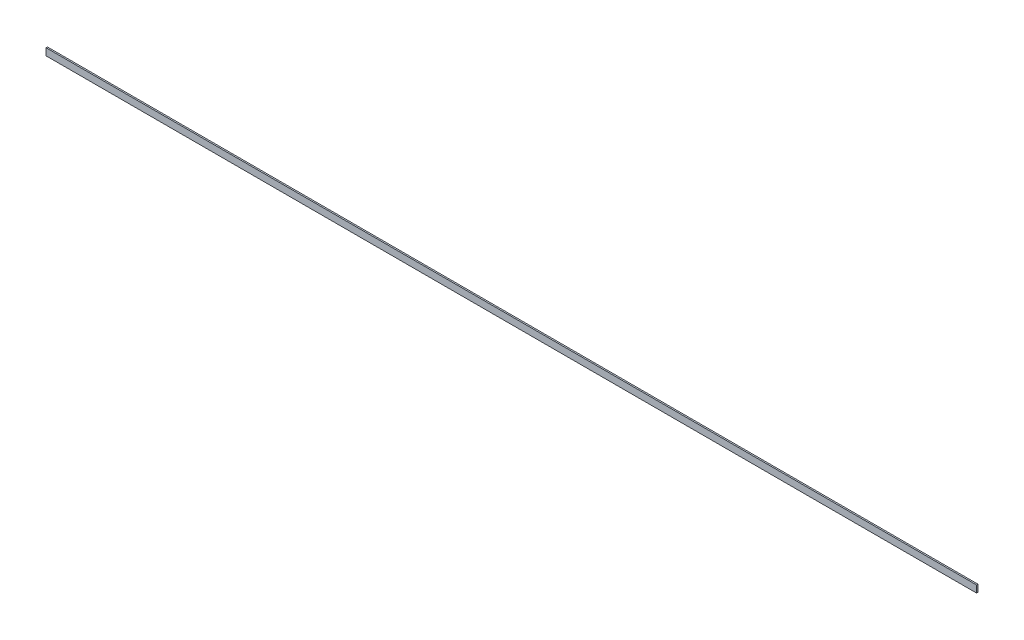
SolidWorks part; units mm, degrees
ref_plane "Спереди" through (0, 0, 0) normal (0, 0, 1) x (1, 0, 0)
ref_plane "Сверху" through (0, 0, 0) normal (0, 1, 0) x (1, 0, 0)
ref_plane "Справа" through (0, 0, 0) normal (1, 0, 0) x (0, 0, -1)
sketch "Эскиз1" plane through (0, 0, 0) normal (1, 0, 0) x (0, 0, -1)
  line L1 (0, 0) -> (4, 0)
  line L2 (0, 0) -> (0, 20)
  line L3 (0, 20) -> (4, 20)
  line L4 (4, 0) -> (4, 20)
extrude "Бобышка-Вытянуть1" add sketch "Эскиз1" along normal blind 2650
